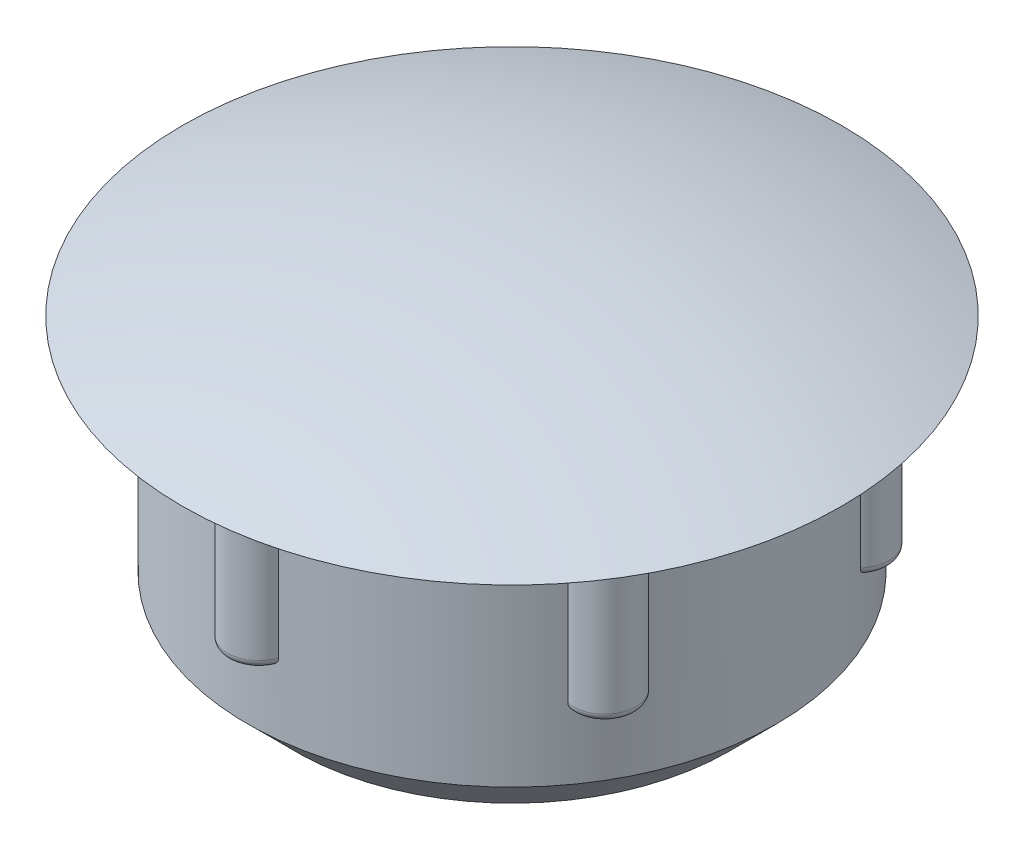
SolidWorks part; units mm, degrees
ref_plane "Спереди" through (0, 0, 0) normal (0, 0, 1) x (1, 0, 0)
ref_plane "Сверху" through (0, 0, 0) normal (0, 1, 0) x (1, 0, 0)
ref_plane "Справа" through (0, 0, 0) normal (1, 0, 0) x (0, 0, -1)
sketch "Эскиз1" plane through (0, 0, 0) normal (0, 0, 1) x (1, 0, 0)
  line L0 (0, 0) -> (0, 1.5) construction
  line L1 (0, 0) -> (8.35, 0) construction
  line L2 (0, 1.5) -> (-7.9019, 1.5) construction
  line L3 (8.35, 0) -> (6.7, 0)
  line L4 (6.7, 0) -> (6.7, -5.6)
  line L5 (6.7, -5.6) -> (5.5, -6.8)
  line L6 (5.5, -6.8) -> (5.5, -0.5)
  line L7 (5.5, -0.5) -> (0, -0.5)
  line L8 (0, -0.5) -> (0, 1.5)
  line L9 (0, -0.5) -> (0, -4.4028) construction
  arc A0 (8.35, 0) -> (0, 1.5) centre (0, -22.4908) ccw
  dimension "D1" = 16.7
  dimension "D2" = 8.3
  dimension "D3" = 45
  dimension "D4" = 13.4
  dimension "D5" = 11
  dimension "D6" = 6.3
  dimension "D7" = 1.5
revolve "Повернуть1" add sketch "Эскиз1" angle 360 about L9
sketch "Эскиз2" plane through (0, 0, 0) normal (0, -1, 0) x (1, 0, 0)
  line L0 (0, 0) -> (2.2024, 0) construction
  line L1 (0, 0) -> (0, 6.7) construction
  circle A0 centre (0, 0) radius 6.7 construction
  arc A1 (-0.75, 6.6579) -> (0.75, 6.6579) centre (0, 6.4101) cw
  circle A2 centre (0, 0) radius 6.7 construction
  arc A3 (-0.75, 6.6579) -> (0.75, 6.6579) centre (0, 0) cw
  dimension "D1" = 14.4
  dimension "D2" = 1.5
extrude "Бобышка-Вытянуть1" add sketch "Эскиз2" along normal blind 4
pattern_circular "Круговой массив1" count 6 over 360 about axis through (0, 0, 0) along (0, 1, 0) of "Бобышка-Вытянуть1"
fillet "Скругление1" radius 0.2 6 edges at (6.2354, -4, 3.6) (6.2354, -4, -3.6) (0, -4, -7.2) (-6.2354, -4, -3.6) (-6.2354, -4, 3.6) (0, -4, 7.2)
